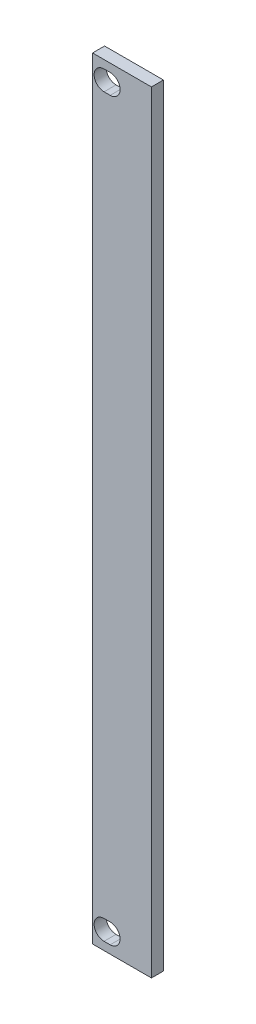
SolidWorks part; units mm, degrees
ref_plane "Front Plane" through (0, 0, 0) normal (0, 0, 1) x (1, 0, 0)
ref_plane "Top Plane" through (0, 0, 0) normal (0, 1, 0) x (1, 0, 0)
ref_plane "Right Plane" through (0, 0, 0) normal (1, 0, 0) x (0, 0, -1)
sketch "Sketch1" plane through (0, 0, 0) normal (0, 0, 1) x (1, 0, 0)
  line L0 (-2.48, 64.25) -> (-2.48, -64.25) construction
  line L1 (-4.9, 64.25) -> (4.9, 64.25)
  line L2 (-4.9, 64.25) -> (-4.9, -64.25)
  line L3 (-4.9, -64.25) -> (4.9, -64.25)
  line L4 (4.9, 64.25) -> (4.9, -64.25)
  line L5 (-4.9, 64.25) -> (4.9, -64.25) construction
  line L6 (-4.9, -64.25) -> (4.9, 64.25) construction
  line L7 (-4.9, 61.25) -> (4.9, 61.25) construction
  line L8 (-4.9, -61.25) -> (4.9, -61.25) construction
  line L9 (-2.988, -61.25) -> (-1.972, -61.25) construction
  line L10 (2.6, 64.25) -> (2.6, -64.25) construction
  line L11 (-2.988, -59.6) -> (-1.972, -59.6)
  line L12 (-2.988, -62.9) -> (-1.972, -62.9)
  line L13 (-2.988, 61.25) -> (-1.972, 61.25) construction
  line L14 (-2.988, 62.9) -> (-1.972, 62.9)
  line L15 (-2.988, 59.6) -> (-1.972, 59.6)
  arc A0 (-2.988, -59.6) -> (-2.988, -62.9) centre (-2.988, -61.25) ccw
  arc A1 (-1.972, -62.9) -> (-1.972, -59.6) centre (-1.972, -61.25) ccw
  arc A2 (-2.988, 62.9) -> (-2.988, 59.6) centre (-2.988, 61.25) ccw
  arc A3 (-1.972, 59.6) -> (-1.972, 62.9) centre (-1.972, 61.25) ccw
  point P0 (0, 0)
  point P18 (-2.48, -61.25)
  point P24 (-2.48, 61.25)
  dimension "D6" = 1.65
  dimension "D7" = 1.65
  dimension "D8" = 1.016
  dimension "D9" = 1.016
  dimension "D1" = 128.5
  dimension "D2" = 9.8
  dimension "D3" = 5.08
  dimension "D4" = 3
  dimension "D10" = 7.5
  dimension "D5" = 3
extrude "Boss-Extrude1" add sketch "Sketch1" along normal blind 2
